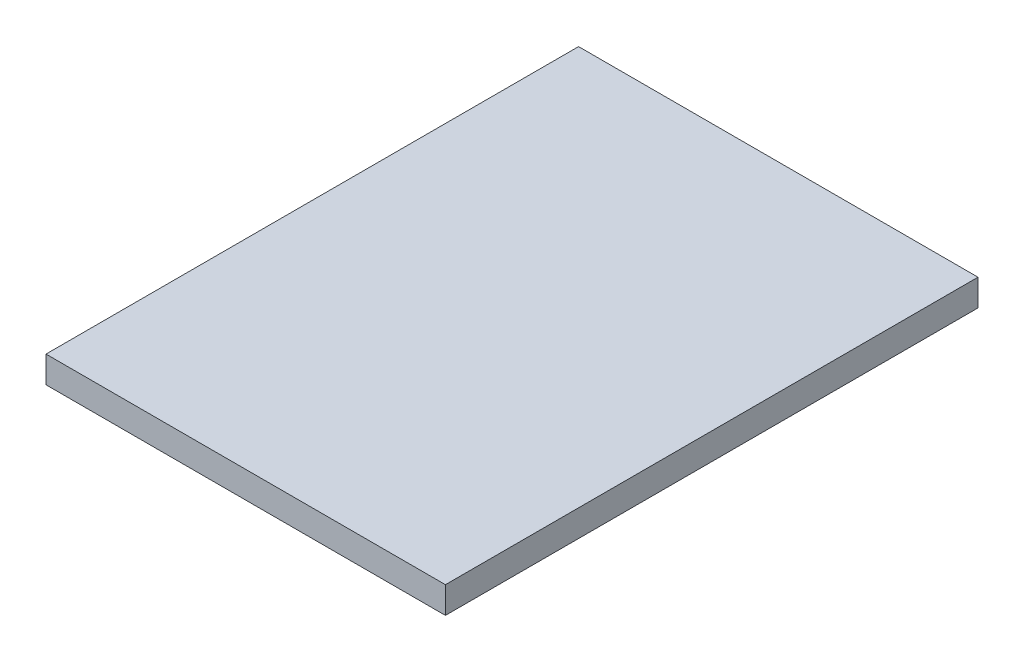
SolidWorks part; units mm, degrees
ref_plane "Front Plane" through (0, 0, 0) normal (0, 0, 1) x (1, 0, 0)
ref_plane "Top Plane" through (0, 0, 0) normal (0, 1, 0) x (1, 0, 0)
ref_plane "Right Plane" through (0, 0, 0) normal (1, 0, 0) x (0, 0, -1)
sketch "Sketch1" plane through (0, 0, 0) normal (0, 1, 0) x (1, 0, 0)
  line L1 (75, -100) -> (-75, -100)
  line L2 (75, -100) -> (75, 100)
  line L3 (75, 100) -> (-75, 100)
  line L4 (-75, -100) -> (-75, 100)
  line L5 (75, -100) -> (-75, 100) construction
  line L6 (75, 100) -> (-75, -100) construction
  point P0 (0, 0)
  dimension "D1" = 150
  dimension "D2" = 200
extrude "Boss-Extrude1" add sketch "Sketch1" along normal blind 10
